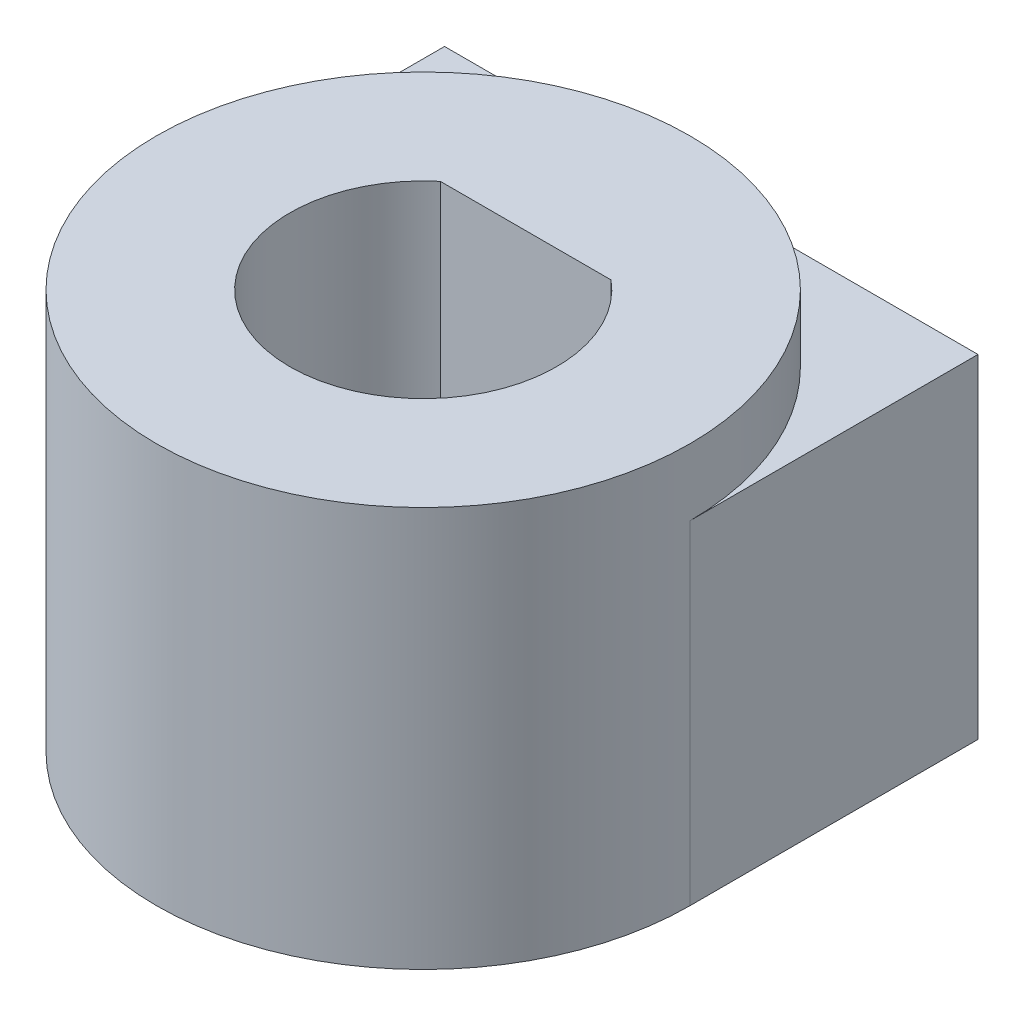
SolidWorks part; units mm, degrees
ref_plane "Front Plane" through (0, 0, 0) normal (0, 0, 1) x (1, 0, 0)
ref_plane "Top Plane" through (0, 0, 0) normal (0, 1, 0) x (1, 0, 0)
ref_plane "Right Plane" through (0, 0, 0) normal (1, 0, 0) x (0, 0, -1)
sketch "Sketch1" plane through (0, 0, 0) normal (0, 1, 0) x (1, 0, 0)
  line L0 (-2.032, 2.4396) -> (2.032, 2.4396)
  line L2 (6.35, 0) -> (-6.35, 0) construction
  line L3 (6.35, 0) -> (6.35, 6.858)
  line L4 (6.35, 6.858) -> (-6.35, 6.858)
  line L5 (-6.35, 0) -> (-6.35, 6.858)
  line L6 (6.35, 0) -> (-6.35, 6.858) construction
  line L7 (6.35, 6.858) -> (-6.35, 0) construction
  circle A0 centre (0, 0) radius 6.35
  circle A1 centre (0, 0) radius 3.175
  point P10 (0, 3.429)
  dimension "D1" = 6.35
  dimension "D2" = 12.7
  dimension "D3" = 4.064
  dimension "D4" = 6.858
  dimension "D5" = 6.35
extrude "Boss-Extrude1" add sketch "Sketch1" along normal blind 7.9375 contours L0 A1 | A0 A1 | A0 L4 L5 | A0 L3 L4
ref_plane "Plane1" through (0, 0, -6.858) normal (0, 0, -1) x (-1, 0, 0)
sketch "Sketch3" plane through (0, 0, -6.858) normal (0, 0, -1) x (-1, 0, 0)
  line L0 (-6.35, 0) -> (6.35, 0) construction
  line L2 (-6.35, 7.9375) -> (-6.35, 0) construction
  circle A0 centre (0, 3.9688) radius 2.7559
  dimension "D1" = 5.5118
  dimension "D2" = 3.9688
  dimension "D3" = 6.35
extrude "Cut-Extrude1" cut sketch "Sketch3" against normal blind 3.81
sketch "Sketch4" plane through (0, 0, -3.048) normal (0, 0, -1) x (-1, 0, 0)
  circle A0 centre (0, 3.9688) radius 1.7526
  dimension "D1" = 3.5052
extrude "Cut-Extrude2" cut sketch "Sketch4" against normal up to next
sketch "Sketch5" plane through (0, 7.9375, 0) normal (0, 1, 0) x (1, 0, 0)
  line L0 (-2.032, 2.4396) -> (2.032, 2.4396)
  arc A0 (2.032, 2.4396) -> (-2.032, 2.4396) centre (0, 0) cw
  arc A1 (-2.032, 2.4396) -> (2.032, 2.4396) centre (0, 0) ccw construction
  circle A2 centre (0, 0) radius 6.35
  dimension "D1" = 12.7
extrude "Boss-Extrude2" add sketch "Sketch5" along normal blind 1.5875
